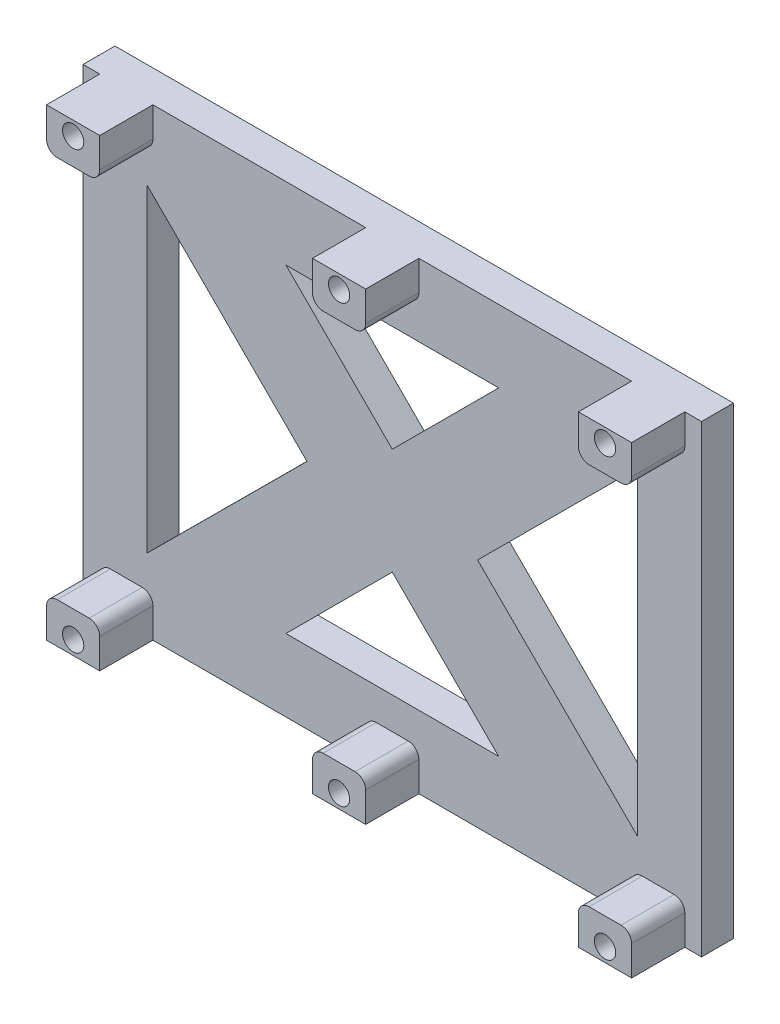
SolidWorks part; units mm, degrees
ref_plane "Front Plane" through (0, 0, 0) normal (0, 0, 1) x (1, 0, 0)
ref_plane "Top Plane" through (0, 0, 0) normal (0, 1, 0) x (1, 0, 0)
ref_plane "Right Plane" through (0, 0, 0) normal (1, 0, 0) x (0, 0, -1)
sketch "Sketch1" plane through (0, 0, 0) normal (0, 0, 1) x (1, 0, 0)
  line L0 (6, 36.7947) -> (6, 6.7947)
  line L1 (0, 0) -> (58.1426, 0)
  line L2 (0, 0) -> (0, 43.5894)
  line L3 (0, 43.5894) -> (58.1426, 43.5894)
  line L4 (58.1426, 0) -> (58.1426, 43.5894)
  line L5 (29.0713, 43.5894) -> (29.0713, 0) construction
  line L7 (39.0713, 6.7947) -> (29.0713, 16.7947)
  line L8 (19.0713, 6.7947) -> (39.0713, 6.7947)
  line L13 (58.1426, 21.7947) -> (0, 21.7947) construction
  line L14 (52.1426, 36.7947) -> (52.1426, 6.7947)
  line L15 (6, 36.7947) -> (21.0529, 21.7947)
  line L16 (21.0529, 21.7947) -> (6, 6.7947)
  line L17 (52.1426, 36.7947) -> (37.0897, 21.7947)
  line L18 (37.0897, 21.7947) -> (52.1426, 6.7947)
  line L19 (19.0713, 36.7947) -> (39.0713, 36.7947)
  line L20 (19.0713, 6.7947) -> (29.0713, 16.7947)
  line L21 (19.0713, 36.7947) -> (29.0713, 26.7947)
  line L22 (39.0713, 36.7947) -> (29.0713, 26.7947)
  point P8 (6, 21.7947)
  point P22 (29.0713, 36.7947)
  point P23 (29.0713, 21.7947)
  dimension "D1" = 6
  dimension "D2" = 46.1426
  dimension "D3" = 43.5894
  dimension "D4" = 30
  dimension "D5" = 21.0529
  dimension "D6" = 21.2506
  dimension "D7" = 20
  dimension "D8" = 10
extrude "Boss-Extrude1" add sketch "Sketch1" along normal blind 3
sketch "Sketch2" plane through (0, 0, 3) normal (0, 0, 1) x (1, 0, 0)
  line L0 (58.1426, 43.5894) -> (0, 43.5894) construction
  line L1 (1.57, 43.5894) -> (6.57, 43.5894)
  line L2 (1.57, 43.5894) -> (1.57, 40.7894)
  line L3 (2.57, 39.7894) -> (5.57, 39.7894)
  line L4 (6.57, 43.5894) -> (6.57, 40.7894)
  line L5 (0, 43.5894) -> (0, 0) construction
  line L6 (0, 21.7947) -> (58.1426, 21.7947) construction
  line L7 (58.1426, 0) -> (58.1426, 43.5894) construction
  line L12 (29.0713, 21.7947) -> (29.0713, 43.5894) construction
  line L13 (26.57, 43.5894) -> (31.57, 43.5894)
  line L14 (26.57, 43.5894) -> (26.57, 40.7894)
  line L15 (27.57, 39.7894) -> (30.57, 39.7894)
  line L16 (31.57, 43.5894) -> (31.57, 40.7894)
  line L17 (51.57, 43.5894) -> (56.57, 43.5894)
  line L18 (51.57, 43.5894) -> (51.57, 40.7894)
  line L19 (52.57, 39.7894) -> (55.57, 39.7894)
  line L20 (56.57, 43.5894) -> (56.57, 40.7894)
  line L21 (56.57, 0) -> (56.57, 2.8)
  line L22 (52.57, 3.8) -> (55.57, 3.8)
  line L23 (51.57, 0) -> (51.57, 2.8)
  line L24 (51.57, 0) -> (56.57, 0)
  line L25 (31.57, 0) -> (31.57, 2.8)
  line L26 (27.57, 3.8) -> (30.57, 3.8)
  line L27 (26.57, 0) -> (26.57, 2.8)
  line L28 (26.57, 0) -> (31.57, 0)
  line L29 (6.57, 0) -> (6.57, 2.8)
  line L30 (2.57, 3.8) -> (5.57, 3.8)
  line L31 (1.57, 0) -> (1.57, 2.8)
  line L32 (1.57, 0) -> (6.57, 0)
  arc A0 (1.57, 40.7894) -> (2.57, 39.7894) centre (2.57, 40.7894) ccw
  arc A1 (6.57, 40.7894) -> (5.57, 39.7894) centre (5.57, 40.7894) cw
  circle A2 centre (4.07, 42.2894) radius 1
  arc A6 (26.57, 40.7894) -> (27.57, 39.7894) centre (27.57, 40.7894) ccw
  arc A7 (31.57, 40.7894) -> (30.57, 39.7894) centre (30.57, 40.7894) cw
  circle A8 centre (29.07, 42.2894) radius 1
  arc A9 (51.57, 40.7894) -> (52.57, 39.7894) centre (52.57, 40.7894) ccw
  arc A10 (56.57, 40.7894) -> (55.57, 39.7894) centre (55.57, 40.7894) cw
  circle A11 centre (54.07, 42.2894) radius 1
  circle A12 centre (54.07, 1.3) radius 1
  arc A13 (56.57, 2.8) -> (55.57, 3.8) centre (55.57, 2.8) ccw
  arc A14 (51.57, 2.8) -> (52.57, 3.8) centre (52.57, 2.8) cw
  circle A15 centre (29.07, 1.3) radius 1
  arc A16 (31.57, 2.8) -> (30.57, 3.8) centre (30.57, 2.8) ccw
  arc A17 (26.57, 2.8) -> (27.57, 3.8) centre (27.57, 2.8) cw
  circle A18 centre (4.07, 1.3) radius 1
  arc A19 (6.57, 2.8) -> (5.57, 3.8) centre (5.57, 2.8) ccw
  arc A20 (1.57, 2.8) -> (2.57, 3.8) centre (2.57, 2.8) cw
  point P12 (6.57, 39.7894)
  point P71 (6.57, 3.8)
  dimension "D2" = 1
  dimension "D5" = 1
  dimension "D6" = 1
  dimension "D1" = 1.57
  dimension "D3" = 2.8
  dimension "D4" = 3
  dimension "D7" = 1.5
  dimension "D8" = 1.5
  dimension "D9" = 3
extrude "Boss-Extrude2" add sketch "Sketch2" along normal blind 5
